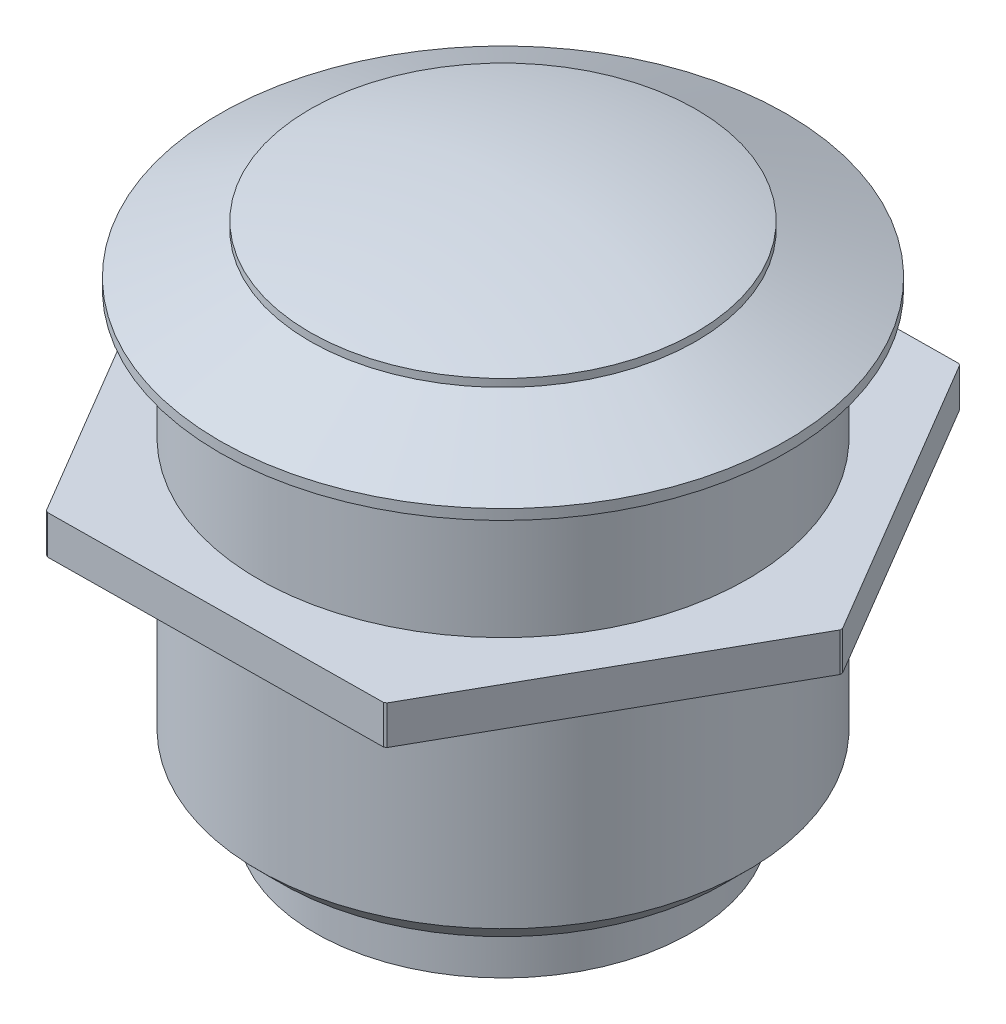
SolidWorks part; units mm, degrees
ref_plane "Front Plane" through (0, 0, 0) normal (0, 0, 1) x (1, 0, 0)
ref_plane "Top Plane" through (0, 0, 0) normal (0, 1, 0) x (1, 0, 0)
ref_plane "Right Plane" through (0, 0, 0) normal (1, 0, 0) x (0, 0, -1)
sketch "Sketch1" plane through (0, 0, 0) normal (0, 0, 1) x (1, 0, 0)
  line L0 (0, 0) -> (0, 14.3838) construction
  line L1 (7.5, -1) -> (7.5, -1.3)
  line L2 (7.5, -1.3) -> (11, -2.9)
  line L3 (11, -2.9) -> (11, -3.3)
  line L4 (11, -3.3) -> (9.5, -3.3)
  line L5 (9.5, -3.3) -> (9.5, -8.3)
  line L6 (9.5, -8.3) -> (13, -8.3)
  line L7 (13, -8.3) -> (13, -9.8)
  line L8 (13, -9.8) -> (9.5, -9.8)
  line L9 (9.5, -9.8) -> (9.5, -18.0887)
  line L10 (9.5, -18.0887) -> (8.5887, -19)
  line L11 (8.5887, -19) -> (7.3, -19)
  line L12 (7.3, -19) -> (7.3, -21.3)
  line L13 (7.3, -21.3) -> (0, -21.3)
  line L14 (0, -21.3) -> (0, 0)
  arc A1 (0, 0) -> (7.5, -1) centre (-0.1833, -29.9994) cw
  dimension "D1" = 15
  dimension "D3" = 1
  dimension "D2" = 30
  dimension "D4" = 0.3
  dimension "D5" = 22
  dimension "D6" = 19
  dimension "D7" = 26
  dimension "D8" = 5
  dimension "D9" = 15.7
  dimension "D10" = 0.4
  dimension "D11" = 1.5
  dimension "D12" = 19
  dimension "D13" = 2
  dimension "D14" = 14.6
  dimension "D15" = 2.3
  dimension "D16" = 135
revolve "Revolve1" add sketch "Sketch1" angle 360 about L0
sketch "Sketch2" plane through (0, -8.3, 0) normal (0, 1, 0) x (1, 0, 0)
  line L0 (-6.619, 11.2143) -> (6.381, 11.3514)
  line L1 (6.4023, 11.3394) -> (13.0211, 0.1496)
  line L2 (13.0213, 0.1251) -> (6.6401, -11.2018)
  line L3 (6.619, -11.2143) -> (-6.381, -11.3514)
  line L4 (-6.4023, -11.3394) -> (-13.0211, -0.1496)
  line L5 (-13.0213, -0.1251) -> (-6.6401, 11.2018)
  arc A0 (6.381, 11.3514) -> (-6.619, 11.2143) centre (0, 0) ccw
  arc A1 (-6.6401, 11.2018) -> (-13.0213, -0.1251) centre (0, 0) ccw
  arc A2 (13.0211, 0.1496) -> (6.4023, 11.3394) centre (0, 0) ccw
  arc A3 (6.6401, -11.2018) -> (13.0213, 0.1251) centre (0, 0) ccw
  arc A4 (-6.381, -11.3514) -> (6.619, -11.2143) centre (0, 0) ccw
  arc A5 (-13.0211, -0.1496) -> (-6.4023, -11.3394) centre (0, 0) ccw
  point P17 (0, 0)
  dimension "D2" = 13
  dimension "D1" = 6
extrude "Cut-Extrude1" cut sketch "Sketch2" against normal through all
